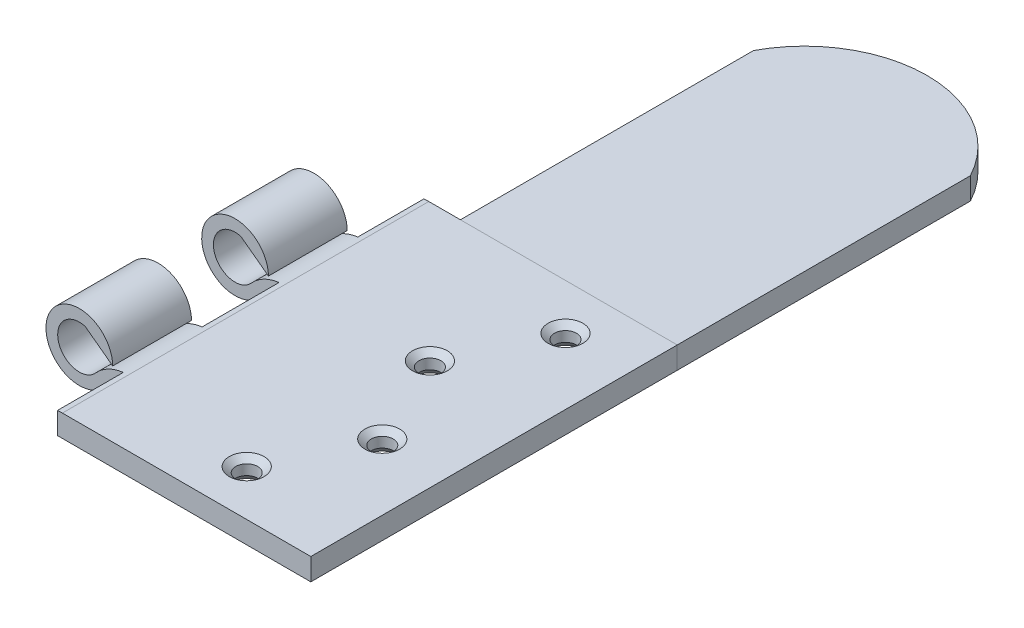
SolidWorks part; units mm, degrees
material "Plain Carbon Steel"
ref_plane "Front Plane" through (0, 0, 0) normal (0, 0, 1) x (1, 0, 0)
ref_plane "Top Plane" through (0, 0, 0) normal (0, 1, 0) x (1, 0, 0)
ref_plane "Right Plane" through (0, 0, 0) normal (1, 0, 0) x (0, 0, -1)
sketch "Sketch1" plane through (0, 0, 0) normal (0, 0, 1) x (1, 0, 0)
  line L0 (5.5871, -2.955) -> (40.5871, -2.955)
  line L1 (6.688, 0.045) -> (40.5871, 0.045)
  line L2 (40.5871, 0.045) -> (40.5871, -2.955)
  line L3 (0, -2.955) -> (40.5871, -2.955) construction
  line L4 (0, 0.045) -> (40.5871, 0.045) construction
  line L5 (4.5548, 0.045) -> (0.7894, 2.8476)
  arc A0 (4.5548, 0.045) -> (2.4111, -3.8645) centre (0, 0) ccw
  arc A1 (0.7894, 2.8476) -> (2.2069, -1.9651) centre (0, 0) ccw
  circle A2 centre (0, 0) radius 4.555 construction
  circle A3 centre (0, 0) radius 2.955 construction
  arc A4 (6.688, 0.045) -> (2.2069, -1.9651) centre (6.688, -5.955) ccw
  arc A5 (5.5871, -2.955) -> (2.4111, -3.8645) centre (5.5871, -8.955) ccw
  dimension "D1" = 9.11
  dimension "D4" = 3
  dimension "D3" = 6
  dimension "D5" = 35
  dimension "D2" = 1.6
extrude "Boss-Extrude1" add sketch "Sketch1" along normal mid plane 50
sketch "Sketch2" plane through (0, 0, 0) normal (0, 1, 0) x (1, 0, 0)
  line L0 (0, 29.25) -> (0, 20.75) construction
  line L2 (0, -29.25) -> (0, -20.75) construction
  line L5 (6, 5.25) -> (-6, 5.25)
  line L6 (6, 5.25) -> (6, -5.25)
  line L7 (6, -5.25) -> (-6, -5.25)
  line L8 (-6, 5.25) -> (-6, -5.25)
  line L9 (6, 5.25) -> (-6, -5.25) construction
  line L10 (6, -5.25) -> (-6, 5.25) construction
  line L11 (6, 25.5) -> (-6, 25.5)
  line L12 (6, 25.5) -> (6, 16)
  line L13 (6, 16) -> (-6, 16)
  line L14 (-6, 25.5) -> (-6, 16)
  line L15 (6, 25.5) -> (-6, 16) construction
  line L16 (6, 16) -> (-6, 25.5) construction
  line L17 (-6, -25.5) -> (6, -25.5)
  line L18 (-6, -25.5) -> (-6, -16)
  line L19 (-6, -16) -> (6, -16)
  line L20 (6, -25.5) -> (6, -16)
  line L21 (-6, -25.5) -> (6, -16) construction
  line L22 (-6, -16) -> (6, -25.5) construction
  point P9 (0, 0)
  dimension "D1" = 8.5
  dimension "D2" = 8.5
  dimension "D3" = 10.5
  dimension "D4" = 12
  dimension "D5" = 9.5
  dimension "D6" = 12
  dimension "D7" = 9.5
  dimension "D8" = 12
  dimension "D9" = 10.75
  dimension "D10" = 10.75
extrude "Cut-Extrude1" cut sketch "Sketch2" against normal blind 6 and the other way blind 6
sketch "Sketch3" plane through (0, 0.045, 0) normal (0, 1, 0) x (1, 0, 0)
  line L0 (40.5871, -25) -> (40.5871, 25) construction
  line L2 (40.5871, -25) -> (6.688, -25) construction
  circle A0 centre (31.5871, 18.75) radius 1.5
  circle A1 centre (25.5871, 6.25) radius 1.5
  circle A2 centre (31.5871, -6.25) radius 1.5
  circle A3 centre (25.5871, -18.75) radius 1.5
  dimension "D1" = 3
  dimension "D2" = 3
  dimension "D3" = 3
  dimension "D4" = 3
  dimension "D5" = 15
  dimension "D6" = 15
  dimension "D7" = 9
  dimension "D8" = 9
  dimension "D9" = 12.5
  dimension "D10" = 12.5
  dimension "D11" = 12.5
  dimension "D12" = 6.25
extrude "Cut-Extrude2" cut sketch "Sketch3" against normal blind 6
chamfer "Chamfer1" distance 0.875 angle 40 8 edges at (25.5871, 0.045, 20.25) (31.5871, 0.045, 7.75) (25.5871, 0.045, -4.75) (31.5871, 0.045, -17.25) (31.5871, -2.955, -17.25) (25.5871, -2.955, -4.75) (31.5871, -2.955, 7.75) (25.5871, -2.955, 20.25)
sketch "Sketch4" plane through (0, -2.955, 0) normal (0, -1, 0) x (1, 0, 0)
  line L0 (6, -25) -> (6, -16) construction
  line L1 (40.5871, -25) -> (11, -25)
  line L2 (40.5871, -25) -> (40.5871, -65)
  line L4 (11, -25) -> (11, -65)
  arc A0 (11, -65) -> (40.5871, -65) centre (25.7936, -57.1442) ccw
  dimension "D3" = 16.75
  dimension "D1" = 5
  dimension "D2" = 40
extrude "Boss-Extrude2" add sketch "Sketch4" against normal blind 3 separate body
